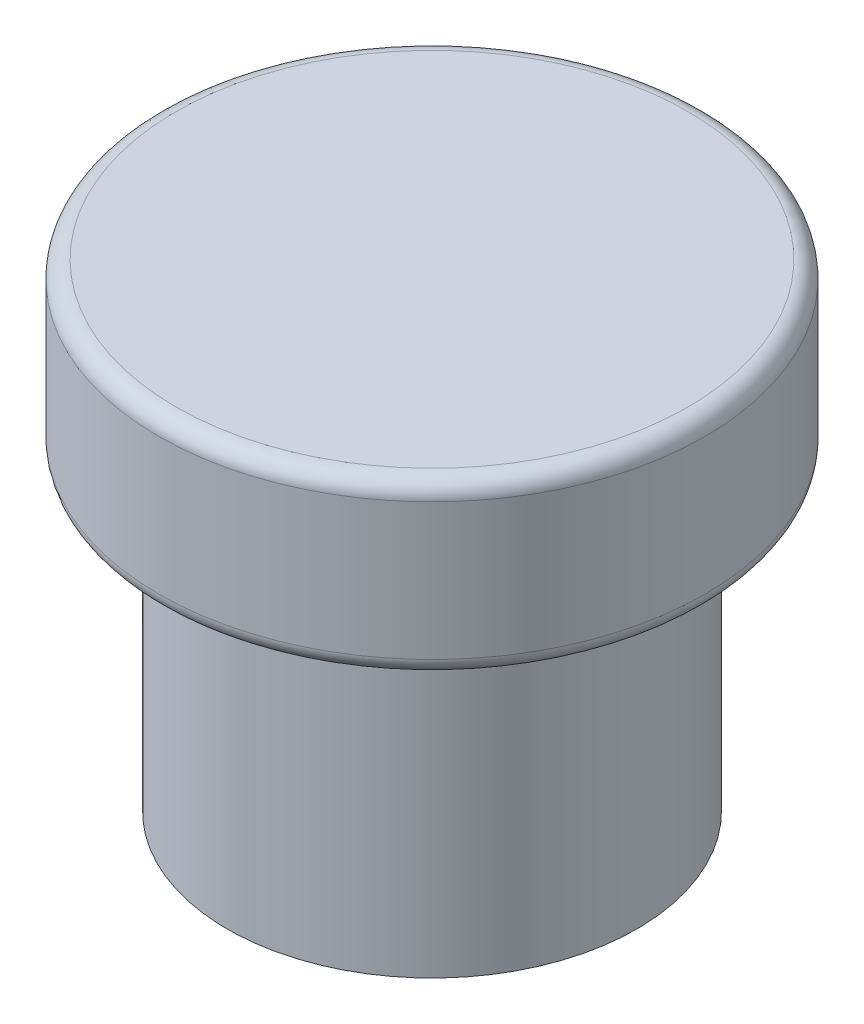
SolidWorks part; units mm, degrees
ref_plane "Front Plane" through (0, 0, 0) normal (0, 0, 1) x (1, 0, 0)
ref_plane "Top Plane" through (0, 0, 0) normal (0, 1, 0) x (1, 0, 0)
ref_plane "Right Plane" through (0, 0, 0) normal (1, 0, 0) x (0, 0, -1)
sketch "Sketch1" plane through (0, 0, 0) normal (1, 0, 0) x (0, 0, -1)
  line L0 (6, 9) -> (8, 9)
  line L1 (0, 0) -> (6, 0)
  line L2 (0, 0) -> (0, 9)
  line L3 (0, 9) -> (6, 9) construction
  line L4 (6, 0) -> (6, 9)
  line L5 (0, 9) -> (8, 9) construction
  line L6 (0, 9) -> (0, 14)
  line L7 (0, 14) -> (8, 14)
  line L8 (8, 9) -> (8, 14)
  dimension "D1" = 5
  dimension "D2" = 6
  dimension "D3" = 9
  dimension "D4" = 8
revolve "Revolve1" add sketch "Sketch1" angle 360 about L2
fillet "Fillet1" radius 0.5 2 edges at (0, 9, -8) (0, 14, -8)
sketch "Sketch2" plane through (0, 0, 0) normal (0, -1, 0) x (1, 0, 0)
  circle A0 centre (0, 0) radius 5.7
  dimension "D1" = 11.4
extrude "Cut-Extrude1" cut sketch "Sketch2" against normal blind 10
